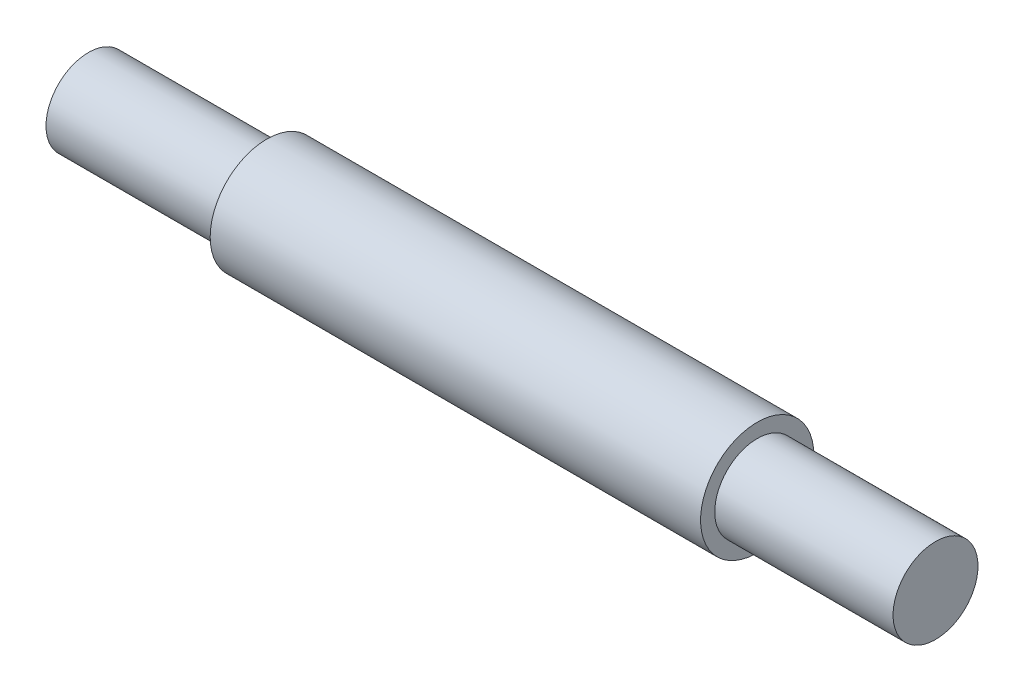
SolidWorks part; units mm, degrees
ref_plane "Front Plane" through (0, 0, 0) normal (0, 0, 1) x (1, 0, 0)
ref_plane "Top Plane" through (0, 0, 0) normal (0, 1, 0) x (1, 0, 0)
ref_plane "Right Plane" through (0, 0, 0) normal (1, 0, 0) x (0, 0, -1)
sketch "Sketch1" plane through (0, 0, 0) normal (1, 0, 0) x (0, 0, -1)
  circle A0 centre (0, 0) radius 6.35
  dimension "D1" = 12.7
extrude "Boss-Extrude1" add sketch "Sketch1" along normal blind 55 and the other way blind 40
sketch "Sketch2" plane through (-40, 0, 0) normal (-1, 0, 0) x (0, 0, 1)
  circle A0 centre (0, 0) radius 4.7625
  dimension "D1" = 9.525
extrude "Cut-Extrude1" cut sketch "Sketch2" against normal blind 20 flip side to cut
cosmetic thread "Cosmetic Thread1" parameters "D2"=7.6327
sketch "Sketch3" plane through (55, 0, 0) normal (1, 0, 0) x (0, 0, -1)
  circle A0 centre (0, 0) radius 4.7625
  dimension "D1" = 9.525
extrude "Cut-Extrude2" cut sketch "Sketch3" against normal blind 20 flip side to cut
cosmetic thread "Cosmetic Thread2" parameters "D2"=7.6327
